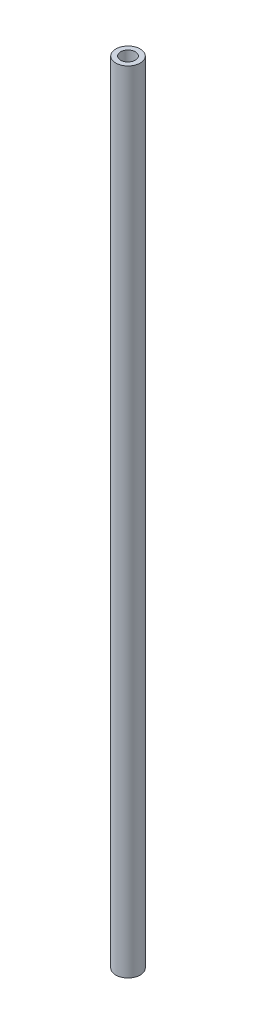
SolidWorks part; units mm, degrees
ref_plane "前视基准面" through (0, 0, 0) normal (0, 0, 1) x (1, 0, 0)
ref_plane "上视基准面" through (0, 0, 0) normal (0, 1, 0) x (1, 0, 0)
ref_plane "右视基准面" through (0, 0, 0) normal (1, 0, 0) x (0, 0, -1)
sketch "草图1" plane through (0, 0, 0) normal (0, 1, 0) x (1, 0, 0)
  circle A0 centre (0, 0) radius 5
  circle A1 centre (0, 0) radius 3
  dimension "D1" = 10
  dimension "D2" = 6
extrude "凸台-拉伸1" add sketch "草图1" along normal blind 323
